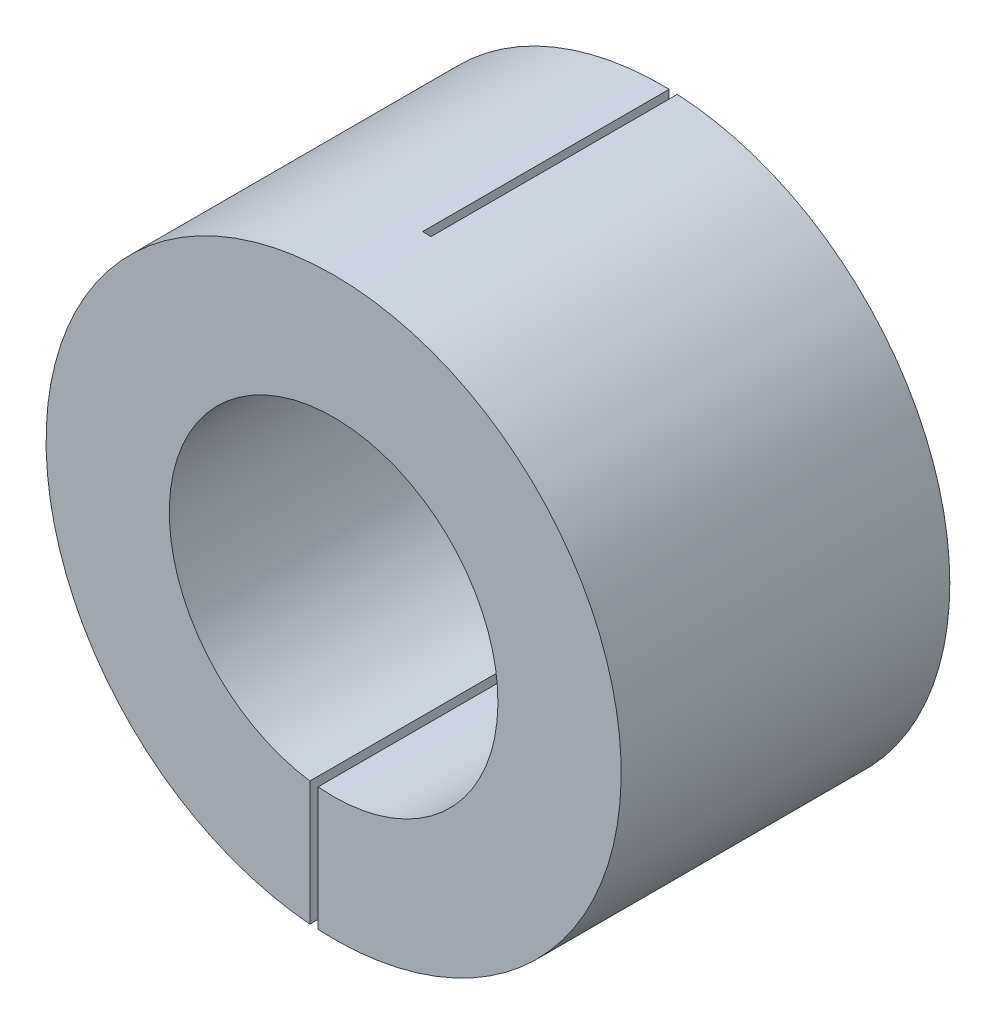
SolidWorks part; units mm, degrees
ref_plane "前视基准面" through (0, 0, 0) normal (0, 0, 1) x (1, 0, 0)
ref_plane "上视基准面" through (0, 0, 0) normal (0, 1, 0) x (1, 0, 0)
ref_plane "右视基准面" through (0, 0, 0) normal (1, 0, 0) x (0, 0, -1)
sketch "草图1" plane through (0, 0, 0) normal (0, 0, 1) x (1, 0, 0)
  circle A0 centre (0, 0) radius 17.5
  circle A1 centre (0, 0) radius 10
  dimension "D1" = 35
  dimension "D2" = 20
extrude "凸台-拉伸1" add sketch "草图1" along normal blind 20
sketch "草图2" plane through (0, 0, 20) normal (0, 0, 1) x (1, 0, 0)
  line L1 (-1.4455, -0.2775) -> (-0.9455, -0.2775)
  line L2 (-1.4455, -0.2775) -> (-1.4455, -19.5791)
  line L3 (-1.4455, -19.5791) -> (-0.9455, -19.5791)
  line L4 (-0.9455, -0.2775) -> (-0.9455, -19.5791)
  line L5 (-1.4455, -0.2775) -> (-0.9455, -19.5791) construction
  line L6 (-1.4455, -19.5791) -> (-0.9455, -0.2775) construction
  circle A0 centre (0, 0) radius 10 construction
  point P0 (-1.1955, -9.9283)
  dimension "D1" = 0.5
extrude "切除-拉伸1" cut sketch "草图2" against normal blind 15
sketch "草图3" plane through (0, 0, 0) normal (0, 0, -1) x (-1, 0, 0)
  line L1 (-0.9197, -2.6864) -> (-0.4197, -2.6864)
  line L2 (-0.9197, -2.6864) -> (-0.9197, 18.127)
  line L3 (-0.9197, 18.127) -> (-0.4197, 18.127)
  line L4 (-0.4197, -2.6864) -> (-0.4197, 18.127)
  line L5 (-0.9197, -2.6864) -> (-0.4197, 18.127) construction
  line L6 (-0.9197, 18.127) -> (-0.4197, -2.6864) construction
  point P0 (-0.6697, 7.7203)
  dimension "D1" = 0.5
extrude "切除-拉伸2" cut sketch "草图3" against normal blind 15
